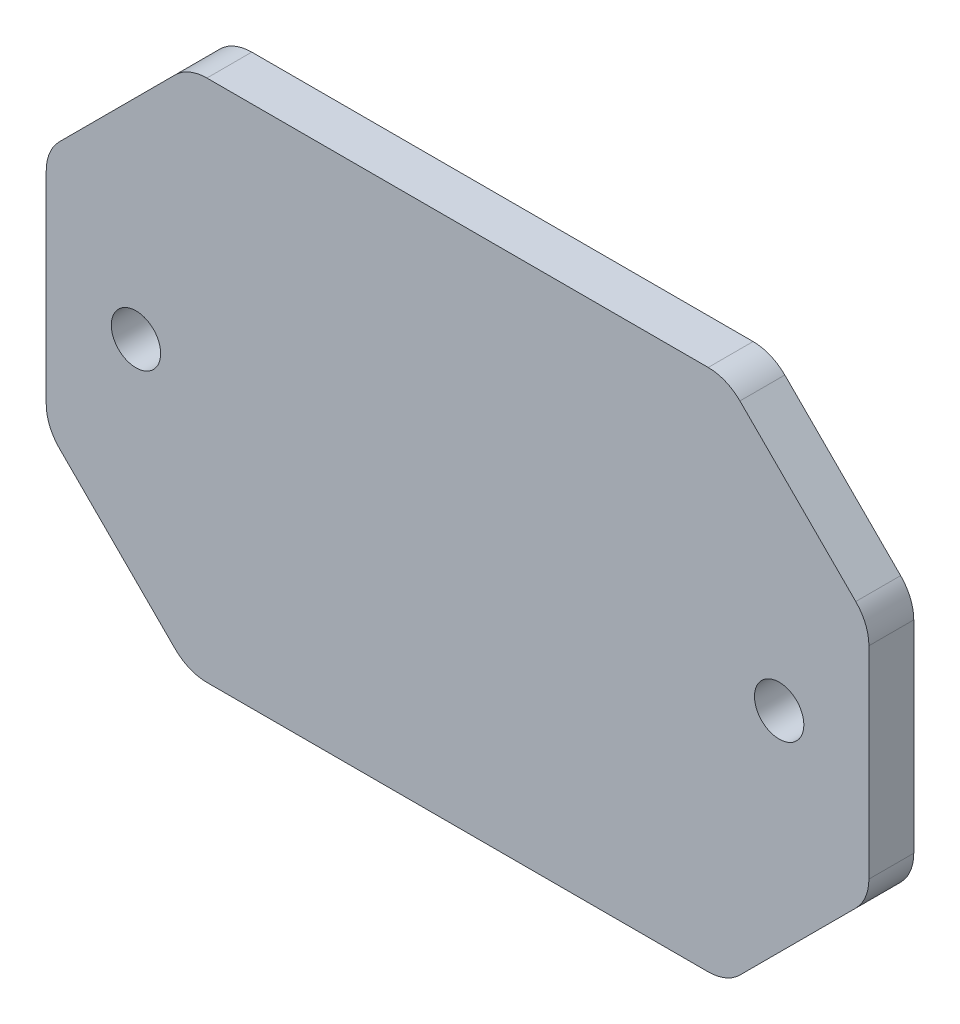
SolidWorks part; units mm, degrees
material "ABS"
ref_plane "前视基准面" through (0, 0, 0) normal (0, 0, 1) x (1, 0, 0)
ref_plane "上视基准面" through (0, 0, 0) normal (0, 1, 0) x (1, 0, 0)
ref_plane "右视基准面" through (0, 0, 0) normal (1, 0, 0) x (0, 0, -1)
sketch "草图1" plane through (0, 0, 0) normal (0, 0, 1) x (1, 0, 0)
  line L1 (-27.5, 17.4981) -> (27.5, 17.4981)
  line L2 (-27.5, 17.4981) -> (-27.5, -17.4981)
  line L3 (-27.5, -17.4981) -> (27.5, -17.4981)
  line L4 (27.5, 17.4981) -> (27.5, -17.4981)
  line L5 (-27.5, 17.4981) -> (27.5, -17.4981) construction
  line L6 (-27.5, -17.4981) -> (27.5, 17.4981) construction
  point P0 (0, 0)
  dimension "D1" = 55
  dimension "D2" = 34.9962
extrude "凸台-拉伸1" add sketch "草图1" along normal blind 3
chamfer "倒角1" distance 9.5 angle 45 4 edges at (-27.5, 17.4981, 1.5) (-27.5, -17.4981, 1.5) (27.5, -17.4981, 1.5) (27.5, 17.4981, 1.5)
fillet "圆角1" radius 3 8 edges at (-27.5, -7.9981, 1.5) (-18, -17.4981, 1.5) (18, -17.4981, 1.5) (27.5, -7.9981, 1.5) (27.5, 7.9981, 1.5) (18, 17.4981, 1.5) (-18, 17.4981, 1.5) (-27.5, 7.9981, 1.5)
sketch "草图2" plane through (0, 0, 3) normal (0, 0, 1) x (1, 0, 0)
  line L0 (-21.5, 0) -> (21.5, 0) construction
  line L1 (27.5, -6.7555) -> (27.5, 6.7555) construction
  line L2 (-27.5, 6.7555) -> (-27.5, -6.7555) construction
  circle A0 centre (-21.5, 0) radius 1.65
  circle A1 centre (21.5, 0) radius 1.65
  dimension "D3" = 3.3
  dimension "D1" = 6
  dimension "D2" = 6
extrude "切除-拉伸1" cut sketch "草图2" against normal through all
